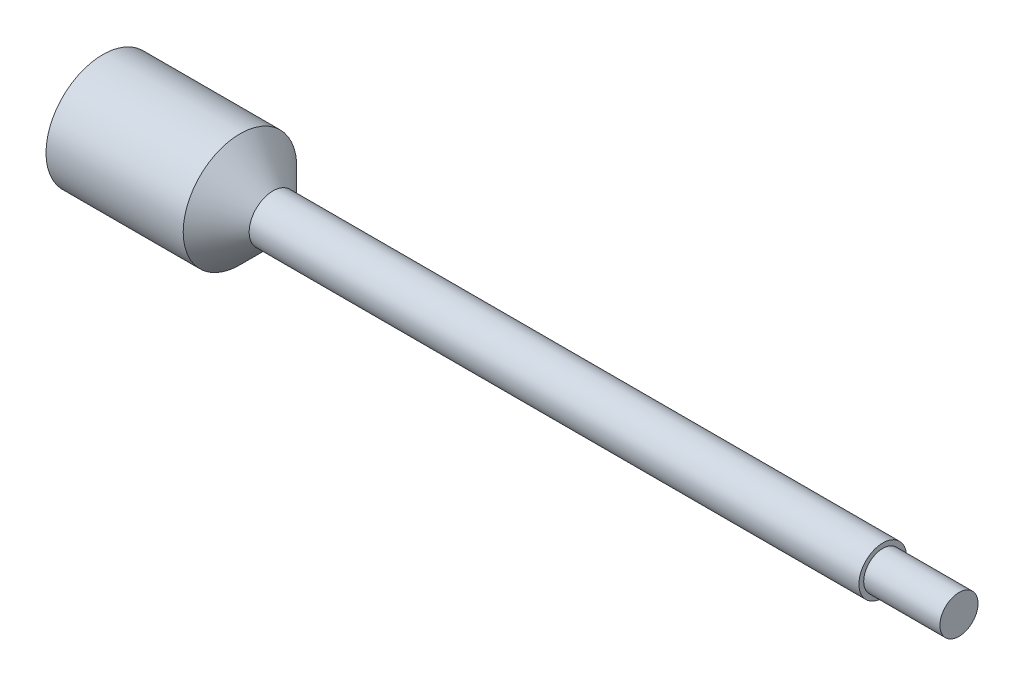
SolidWorks part; units mm, degrees
ref_plane "Front Plane" through (0, 0, 0) normal (0, 0, 1) x (1, 0, 0)
ref_plane "Top Plane" through (0, 0, 0) normal (0, 1, 0) x (1, 0, 0)
ref_plane "Right Plane" through (0, 0, 0) normal (1, 0, 0) x (0, 0, -1)
sketch "Sketch1" plane through (0, 0, 0) normal (0, 0, 1) x (1, 0, 0)
  line L0 (-55.8412, 0) -> (86.8116, 0) construction
  line L1 (-55.8412, -9.4615) -> (-55.8412, 9.4615)
  line L2 (-55.8412, 9.4615) -> (-32.9812, 9.4615)
  line L3 (-32.9812, 9.4615) -> (-27.4884, 3.9688)
  line L4 (-27.4884, 3.9688) -> (74.1116, 3.9688)
  line L5 (74.1116, 3.9688) -> (74.1116, 3.175)
  line L6 (74.1116, 3.175) -> (86.8116, 3.175)
  line L7 (86.8116, 3.175) -> (86.8116, -3.175)
  line L8 (74.1116, -3.175) -> (86.8116, -3.175)
  line L9 (74.1116, -3.9688) -> (74.1116, -3.175)
  line L10 (-27.4884, -3.9688) -> (74.1116, -3.9688)
  line L11 (-32.9812, -9.4615) -> (-27.4884, -3.9688)
  line L12 (-55.8412, -9.4615) -> (-32.9812, -9.4615)
  dimension "D1" = 18.923
  dimension "D2" = 7.9375
  dimension "D3" = 6.35
  dimension "D4" = 101.6
  dimension "D5" = 22.86
  dimension "D6" = 12.7
  dimension "D7" = 45
revolve "Revolve1" add sketch "Sketch1" angle 360 about L0
